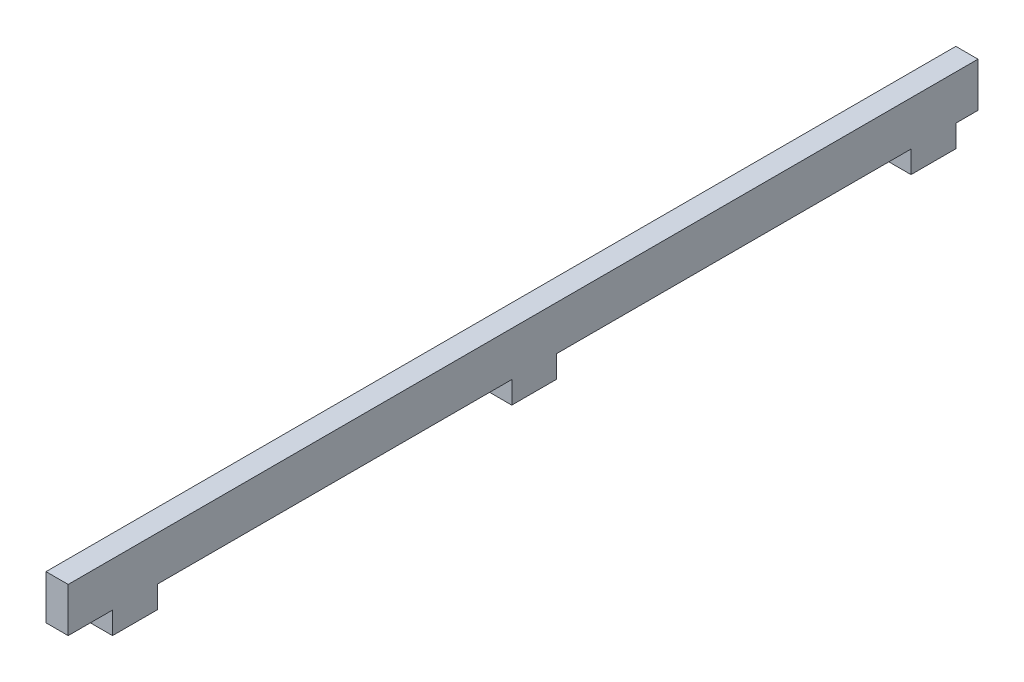
SolidWorks part; units mm, degrees
ref_plane "Front Plane" through (0, 0, 0) normal (0, 0, 1) x (1, 0, 0)
ref_plane "Top Plane" through (0, 0, 0) normal (0, 1, 0) x (1, 0, 0)
ref_plane "Right Plane" through (0, 0, 0) normal (1, 0, 0) x (0, 0, -1)
sketch "Sketch1" plane through (0, 0, 0) normal (1, 0, 0) x (0, 0, -1)
  line L0 (0, 0) -> (0, -12.7)
  line L1 (0, -12.7) -> (12.7, -12.7)
  line L2 (12.7, -12.7) -> (12.7, -19.05)
  line L3 (12.7, -19.05) -> (25.527, -19.05)
  line L4 (25.527, -19.05) -> (25.527, -12.7)
  line L5 (25.527, -12.7) -> (127, -12.7)
  line L6 (127, -12.7) -> (127, -19.05)
  line L7 (127, -19.05) -> (139.827, -19.05)
  line L8 (139.827, -19.05) -> (139.827, -12.7)
  line L9 (139.827, -12.7) -> (241.3, -12.7)
  line L10 (241.3, -12.7) -> (241.3, -19.05)
  line L11 (241.3, -19.05) -> (254.127, -19.05)
  line L12 (254.127, -19.05) -> (254.127, -12.7)
  line L13 (254.127, -12.7) -> (260.477, -12.7)
  line L14 (254.127, -12.7) -> (355.6, -12.7) [skipped]
  line L15 (0, 0) -> (260.477, 0)
  line L16 (260.477, 0) -> (260.477, -12.7)
  dimension "D1" = 12.827
  dimension "D2" = 6.35
  dimension "D3" = 6.35
  dimension "D4" = 12.7
  dimension "D5" = 114.3
  dimension "D7" = 6.35
  dimension "D8" = 12.7
  dimension "D6" = 3
extrude "Boss-Extrude1" add sketch "Sketch1" along normal blind 6.35
